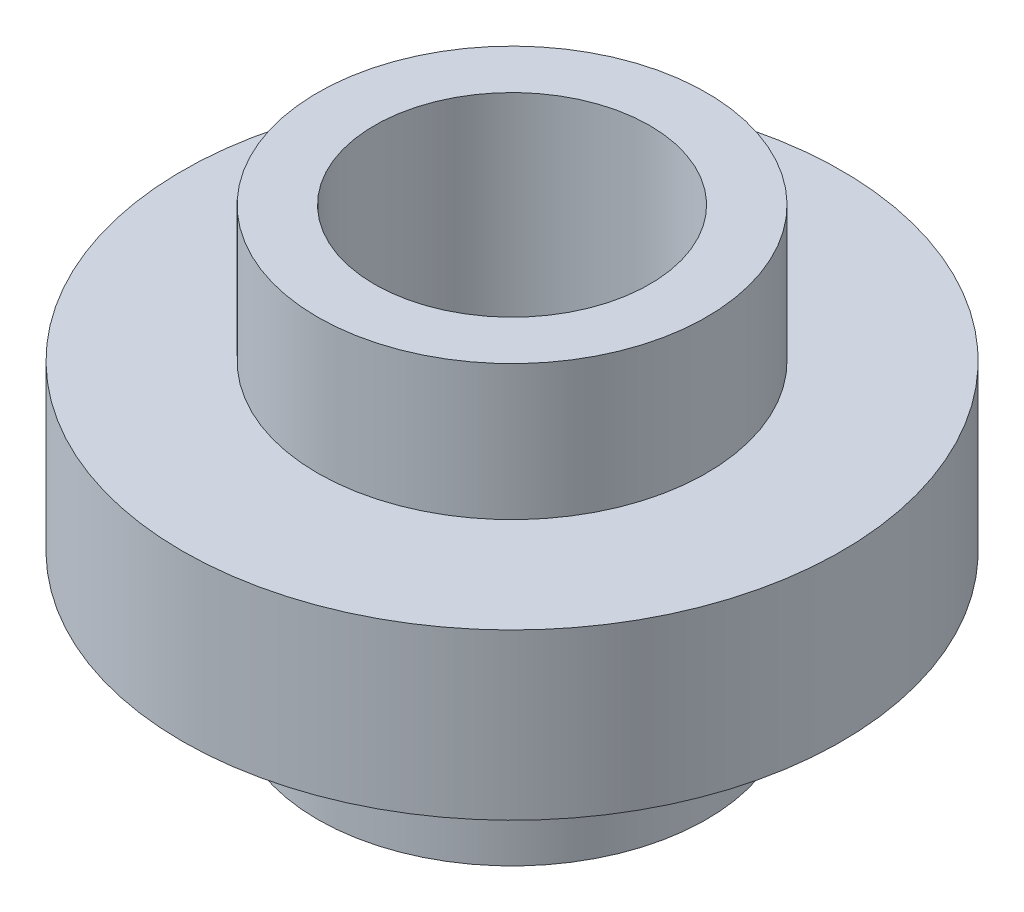
SolidWorks part; units mm, degrees
ref_plane "Piano frontale" through (0, 0, 0) normal (0, 0, 1) x (1, 0, 0)
ref_plane "Piano superiore" through (0, 0, 0) normal (0, 1, 0) x (1, 0, 0)
ref_plane "Piano destro" through (0, 0, 0) normal (1, 0, 0) x (0, 0, -1)
sketch "Schizzo2" plane through (0, 0, 0) normal (1, 0, 0) x (0, 0, -1)
  line L0 (0, 6.6) -> (0, -6.6)
  line L1 (0, 6.6) -> (5.9, 6.6)
  line L2 (5.9, 6.6) -> (5.9, 2.5)
  line L3 (5.9, 2.5) -> (10, 2.5)
  line L4 (10, 2.5) -> (10, -2.5)
  line L5 (10, -2.5) -> (5.9, -2.5)
  line L6 (5.9, -2.5) -> (5.9, -6.6)
  line L7 (5.9, -6.6) -> (0, -6.6)
  point P0 (0, 0)
  point P1 (10, -2.5)
  dimension "D1" = 13.2
  dimension "D2" = 10
  dimension "D3" = 5
  dimension "D4" = 4.1
  dimension "D5" = 5.9
revolve "Rivoluzione1" add sketch "Schizzo2" angle 360 about L0
sketch "Schizzo5" plane through (0, 6.6, 0) normal (0, 1, 0) x (1, 0, 0)
  circle A0 centre (0, 0) radius 4.175
  dimension "D1" = 8.35
extrude "Taglio-Estrusione1" cut sketch "Schizzo5" against normal through all
